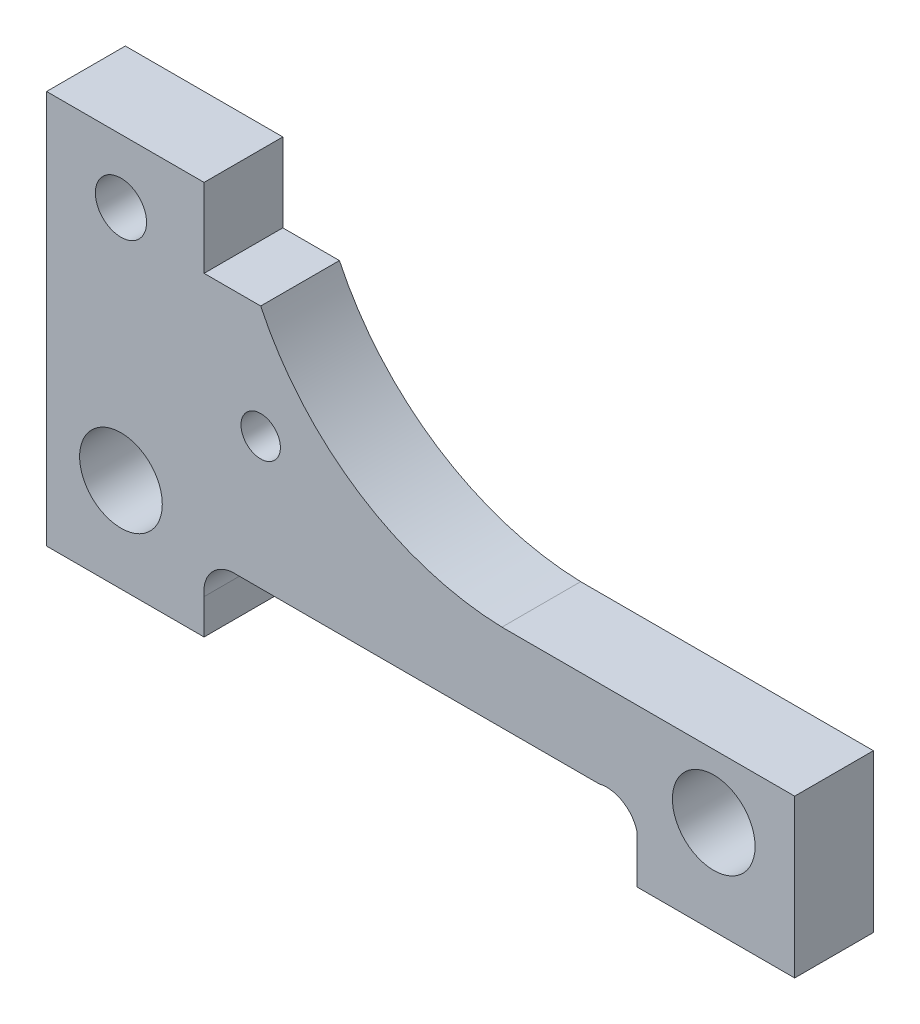
SolidWorks part; units mm, degrees
ref_plane "Front Plane" through (0, 0, 0) normal (0, 0, 1) x (1, 0, 0)
ref_plane "Top Plane" through (0, 0, 0) normal (0, 1, 0) x (1, 0, 0)
ref_plane "Right Plane" through (0, 0, 0) normal (1, 0, 0) x (0, 0, -1)
sketch "Sketch1" plane through (0, 0, 0) normal (0, 0, 1) x (1, 0, 0)
  line L0 (-42.2222, -7.7778) -> (52.7778, -7.7778) construction
  line L1 (-42.2222, -7.7778) -> (-42.2222, 42.2222)
  line L2 (-42.2222, 42.2222) -> (-22.2222, 42.2222)
  line L3 (-22.2222, 42.2222) -> (-22.2222, 32.2222)
  line L4 (-22.2222, 32.2222) -> (-15.0335, 32.2222)
  line L5 (-42.2222, -7.7778) -> (-22.2222, -7.7778)
  line L9 (32.7778, -7.7778) -> (52.7778, -7.7778)
  line L10 (52.7778, -7.7778) -> (52.7778, 12.2222)
  line L11 (52.7778, 12.2222) -> (15.6024, 12.2222)
  line L12 (-32.7778, 34.1667) -> (-32.7778, 4.1667) construction
  line L13 (-22.2222, -7.7778) -> (-22.2222, -3.3333)
  line L14 (32.7778, -7.7778) -> (32.7778, -1.7591)
  line L15 (-18.7765, 1.153) -> (27.928, 1.153)
  arc A0 (-15.0335, 32.2222) -> (15.6024, 12.2222) centre (16.596, 47.2081) ccw
  circle A1 centre (-32.7778, 34.1667) radius 3.25
  circle A2 centre (-32.7778, 4.1667) radius 5.25
  circle A3 centre (-15.0335, 17.9005) radius 2.5
  circle A4 centre (42.5, 4.1667) radius 5.25
  arc A5 (-22.2222, -3.3333) -> (-18.7765, 1.153) centre (-18.2562, -2.813) cw
  arc A6 (32.7778, -1.7591) -> (27.928, 1.153) centre (28.8969, -2.7279) ccw
  dimension "D3" = 35
  dimension "D7" = 6.5
  dimension "D8" = 10.5
  dimension "D9" = 10.5
  dimension "D10" = 5
  dimension "D11" = 4
  dimension "D12" = 4
  dimension "D1" = 95
  dimension "D2" = 50
  dimension "D4" = 20
  dimension "D5" = 10
  dimension "D6" = 30
extrude "Boss-Extrude1" add sketch "Sketch1" along normal blind 10
